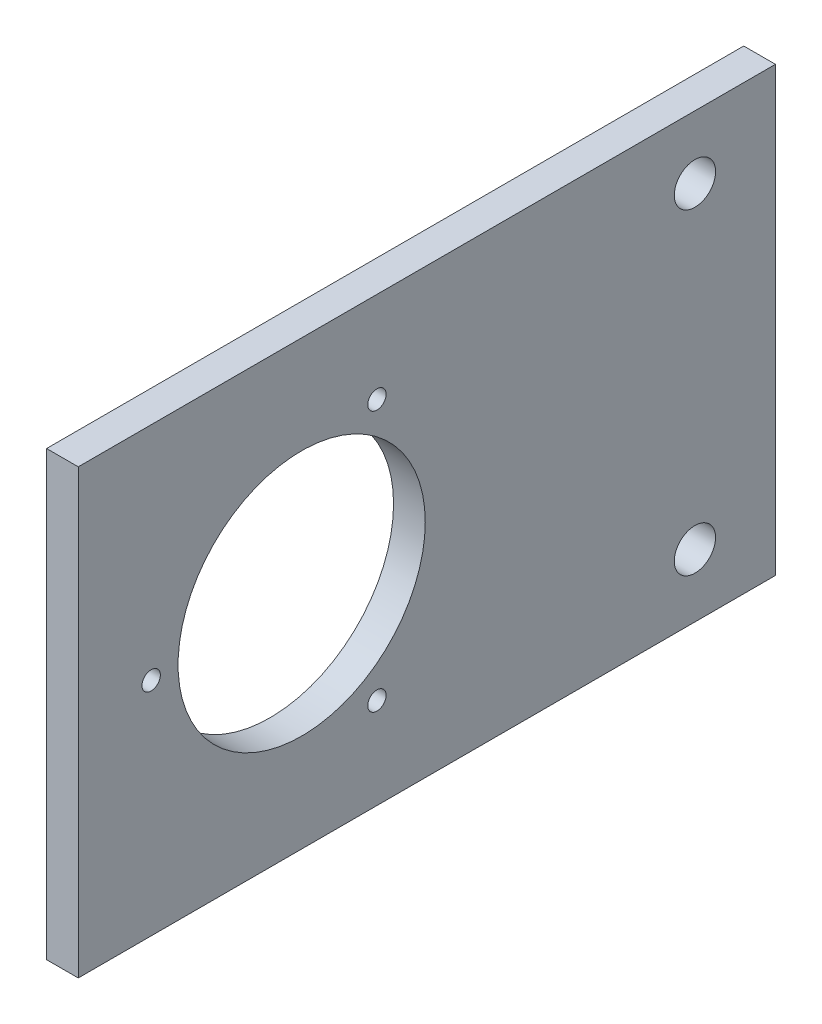
SolidWorks part; units mm, degrees
ref_plane "Front Plane" through (0, 0, 0) normal (1, 0, 0) x (0, 1, 0)
ref_plane "Top Plane" through (0, 0, 0) normal (0, 0, 1) x (0, 1, 0)
ref_plane "Right Plane" through (0, 0, 0) normal (0, 1, 0) x (-1, 0, 0)
sketch "Sketch1" plane through (0, 0, 0) normal (1, 0, 0) x (0, 1, 0)
  line L0 (-34.925, 19.75) -> (34.925, 19.75) construction
  line L1 (-34.925, -55) -> (34.925, -55)
  line L2 (-34.925, -55) -> (-34.925, 55)
  line L3 (-34.925, 55) -> (34.925, 55)
  line L4 (34.925, -55) -> (34.925, 55)
  line L5 (-34.925, -55) -> (34.925, 55) construction
  line L6 (-34.925, 55) -> (34.925, -55) construction
  line L7 (0, 55) -> (0, -55) construction
  line L8 (-34.925, -42.3) -> (34.925, -42.3) construction
  line L9 (0, 19.75) -> (0, 43.5) construction
  line L10 (20.5681, 7.875) -> (0, 19.75) construction
  line L11 (0, 19.75) -> (-20.5681, 7.875) construction
  circle A5 centre (0, 19.75) radius 19.5
  circle A6 centre (-25, -42.3) radius 3.2576
  circle A7 centre (25, -42.3) radius 3.2576
  circle A8 centre (-20.5681, 7.875) radius 1.45
  circle A9 centre (20.5681, 7.875) radius 1.45
  circle A10 centre (0, 43.5) radius 1.45
  point P0 (0, 0)
  dimension "D5" = 2.9
  dimension "D4" = 23.75
  dimension "D6" = 120
  dimension "D8" = 39
  dimension "D10" = 6.5151
  dimension "D1" = 110
  dimension "D2" = 69.85
  dimension "D3" = 74.75
  dimension "D7" = 120
  dimension "D9" = 12.7
  dimension "D11" = 25
extrude "Boss-Extrude1" add sketch "Sketch1" along normal blind 5
